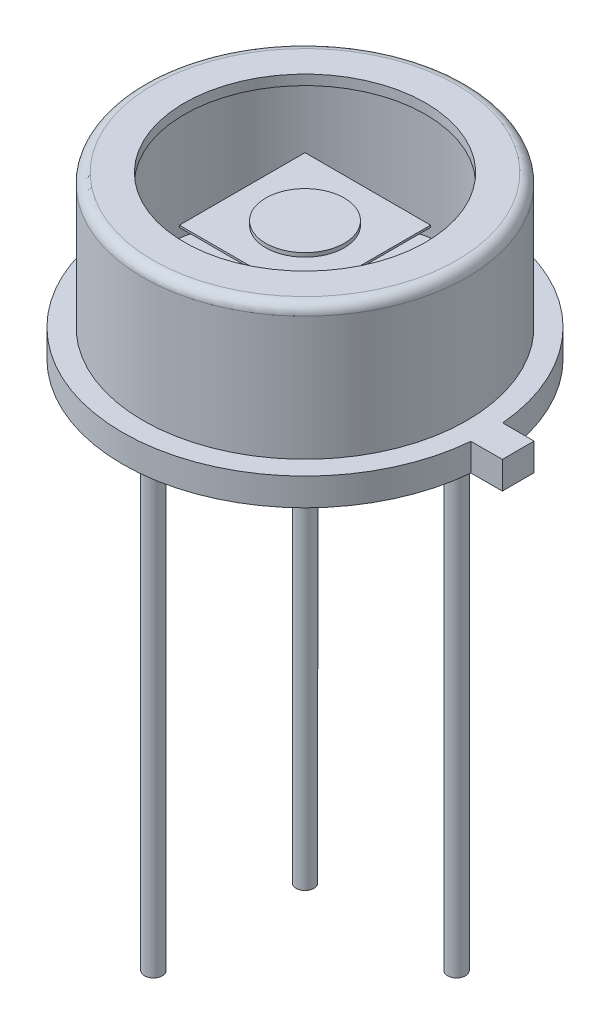
SolidWorks part; units mm, degrees
ref_plane "Front Plane" through (0, 0, 0) normal (0, 0, 1) x (1, 0, 0)
ref_plane "Top Plane" through (0, 0, 0) normal (0, 1, 0) x (1, 0, 0)
ref_plane "Right Plane" through (0, 0, 0) normal (1, 0, 0) x (0, 0, -1)
sketch "Sketch1" plane through (0, 0, 0) normal (0, 0, 1) x (1, 0, 0)
  line L0 (0, 0) -> (0, 37.7864) construction
  line L2 (4.65, 0) -> (4.65, 0.7)
  line L3 (4.65, 0.7) -> (4.125, 0.7)
  line L6 (4.125, 0.7) -> (4.125, 3.856)
  line L7 (3.871, 4.11) -> (3.075, 4.11)
  arc A0 (4.125, 3.856) -> (3.871, 4.11) centre (3.871, 3.856) ccw
  dimension "D7" = 0.254
  dimension "D1" = 0.7
  dimension "D2" = 8.25
  dimension "D4" = 9.3
  dimension "D6" = 4.11
  dimension "D8" = 6.15
revolve "Revolve-Thin2" add sketch "Sketch1" angle 360 about L0
sketch "Sketch2" plane through (0, 0, 0) normal (0, -1, 0) x (1, 0, 0)
  circle A1 centre (0, 0) radius 4.65
  circle A2 centre (0, 0) radius 4.65
  dimension "D1" = 0
extrude "Boss-Extrude1" add sketch "Sketch2" against normal up to surface (0.446 mm away) up to face at (0, 0.446, -3.871)
sketch "Sketch3" plane through (0, 0, 0) normal (0, -1, 0) x (1, 0, 0)
  line L0 (1.6, 1.6) -> (-1.6, -1.6) construction
  line L1 (-1.6, 1.6) -> (1.6, 1.6)
  line L2 (-1.6, 1.6) -> (-1.6, -1.6)
  line L3 (-1.6, -1.6) -> (1.6, -1.6)
  line L4 (1.6, 1.6) -> (1.6, -1.6)
  dimension "D1" = 3.2
extrude "Boss-Extrude2" add sketch "Sketch3" along normal blind 0.05 from offset 2.95 separate body offset against normal yes
sketch "Sketch8" plane through (0, 2.95, 0) normal (0, 1, 0) x (-1, 0, 0)
  circle A0 centre (0, 0) radius 1
  dimension "D1" = 2
extrude "Boss-Extrude6" add sketch "Sketch8" along normal blind 0.1
sketch "Sketch11" plane through (0, 0, 0) normal (0, -1, 0) x (1, 0, 0)
  line L0 (0, 0) -> (6.1157, 0) construction
  line L1 (5.4323, 0) -> (5.4323, -0.405)
  line L2 (5.4323, -0.405) -> (4.6323, -0.405)
  line L3 (5.4323, 0) -> (5.4323, 0.405)
  line L4 (5.4323, 0.405) -> (4.6323, 0.405)
  line L5 (0, 0) -> (0, 6.1969) construction
  circle A0 centre (0, 0) radius 4.57
  circle A1 centre (0, 0) radius 4.65 construction
  circle M1 centre (0, 0) radius 4.65
  dimension "D4" = 9.14
  dimension "D1" = 0.405
  dimension "D2" = 0.8
  dimension "D3" = 270
  dimension "D5" = 0.405
extrude "Boss-Extrude8" add sketch "Sketch11" against normal up to surface (0.7 mm away) contours L3 L4 L2 L1 M1 up to face at (0, 0.7, -4.125)
sketch "Sketch5" plane through (0, 0, 0) normal (0, -1, 0) x (1, 0, 0)
  line L0 (0, 0) -> (-1.9304, 1.9304) construction
  line L1 (0, 0) -> (2.73, 0) construction
  line L2 (0, 1.6552) -> (0, -1.2761) construction
  circle A0 centre (0, 0) radius 2.73 construction
  circle A2 centre (1.9304, -1.9304) radius 0.23
  circle A3 centre (-1.9304, 1.9304) radius 0.23
  circle A4 centre (-1.9304, -1.9304) radius 0.23
  circle A5 centre (1.9304, 1.9304) radius 0.23 [skipped]
  dimension "D1" = 5.46
  dimension "D2" = 135
  dimension "D3" = 4
  dimension "D5" = 0.46
extrude "Boss-Extrude4" add sketch "Sketch5" along normal blind 13.5
sketch "Sketch7" plane through (0, 0, 0) normal (0, -1, 0) x (1, 0, 0)
  circle A0 centre (-1.9304, 1.9304) radius 0.75
  dimension "D1" = 1.5
extrude "Boss-Extrude5" [suppressed] add sketch "Sketch7" along normal blind 0.4
sketch "Sketch9" plane through (0, 0, 0) normal (0, -1, 0) x (1, 0, 0)
  circle A0 centre (0, -3.8) radius 0.5
  dimension "D1" = 1
  dimension "D2" = 3.8
extrude "Boss-Extrude7" [suppressed] add sketch "Sketch9" along normal blind 0.01
